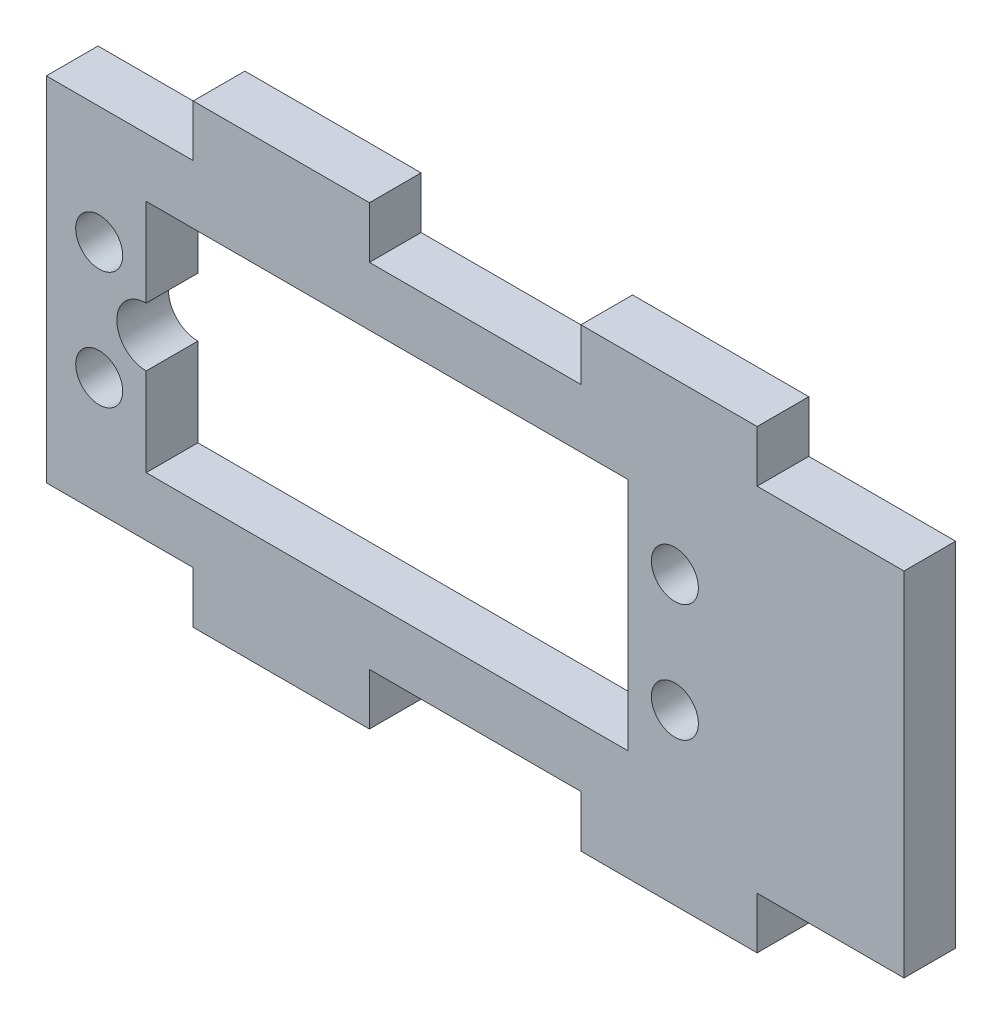
SolidWorks part; units mm, degrees
ref_plane "前视基准面" through (0, 0, 0) normal (0, 0, 1) x (1, 0, 0)
ref_plane "上视基准面" through (0, 0, 0) normal (0, 1, 0) x (1, 0, 0)
ref_plane "右视基准面" through (0, 0, 0) normal (1, 0, 0) x (0, 0, -1)
sketch "草图1" plane through (0, 0, 0) normal (0, 0, 1) x (1, 0, 0)
  line L0 (9, 15) -> (9, 19.4)
  line L1 (-36.5, 0) -> (36.5, 0) construction
  line L2 (0, -15) -> (0, 15) construction
  line L3 (-9, 15) -> (9, 15)
  line L4 (36.5, -15) -> (36.5, 15)
  line L5 (9, 19.4) -> (24, 19.4)
  line L6 (24, 19.4) -> (24, 15)
  line L7 (24, 15) -> (36.5, 15)
  line L8 (24, -15) -> (36.5, -15)
  line L9 (24, -19.4) -> (24, -15)
  line L10 (9, -19.4) -> (24, -19.4)
  line L11 (-9, -15) -> (9, -15)
  line L12 (9, -15) -> (9, -19.4)
  line L13 (-9, -15) -> (-9, -19.4)
  line L14 (-9, -19.4) -> (-24, -19.4)
  line L15 (-24, -19.4) -> (-24, -15)
  line L16 (-24, -15) -> (-36.5, -15)
  line L17 (-24, 15) -> (-36.5, 15)
  line L18 (-24, 19.4) -> (-24, 15)
  line L19 (-9, 19.4) -> (-24, 19.4)
  line L20 (-36.5, -15) -> (-36.5, 15)
  line L21 (-9, 15) -> (-9, 19.4)
  line L22 (13, 10) -> (-28, 10)
  line L23 (13, 10) -> (13, -10)
  line L24 (-28, 10) -> (-28, -10)
  line L25 (13, -10) -> (-28, -10)
  line L26 (-7.5, 10) -> (-7.5, -10) construction
  circle A0 centre (-32, 5) radius 2
  circle A1 centre (-32, -5) radius 2
  circle A2 centre (17, -5) radius 2
  circle A3 centre (17, 5) radius 2
  point P16 (0, 0)
  point P31 (-28, 0)
  point P32 (13, 0)
  dimension "D11" = 4
  dimension "D1" = 30
  dimension "D2" = 73
  dimension "D3" = 4.4
  dimension "D4" = 18
  dimension "D5" = 15
  dimension "D6" = 41
  dimension "D7" = 20
  dimension "D8" = 28
  dimension "D9" = 10
  dimension "D10" = 49
extrude "凸台-拉伸1" add sketch "草图1" along normal blind 4.4
sketch "草图2" plane through (0, 0, 4.4) normal (0, 0, 1) x (1, 0, 0)
  line L0 (-32, 5) -> (-32, -5) construction
  line L1 (-28, 10) -> (-28, -10) construction
  circle A0 centre (-28, 0) radius 2.5
  dimension "D1" = 5
extrude "切除-拉伸1" cut sketch "草图2" against normal blind 4.4
